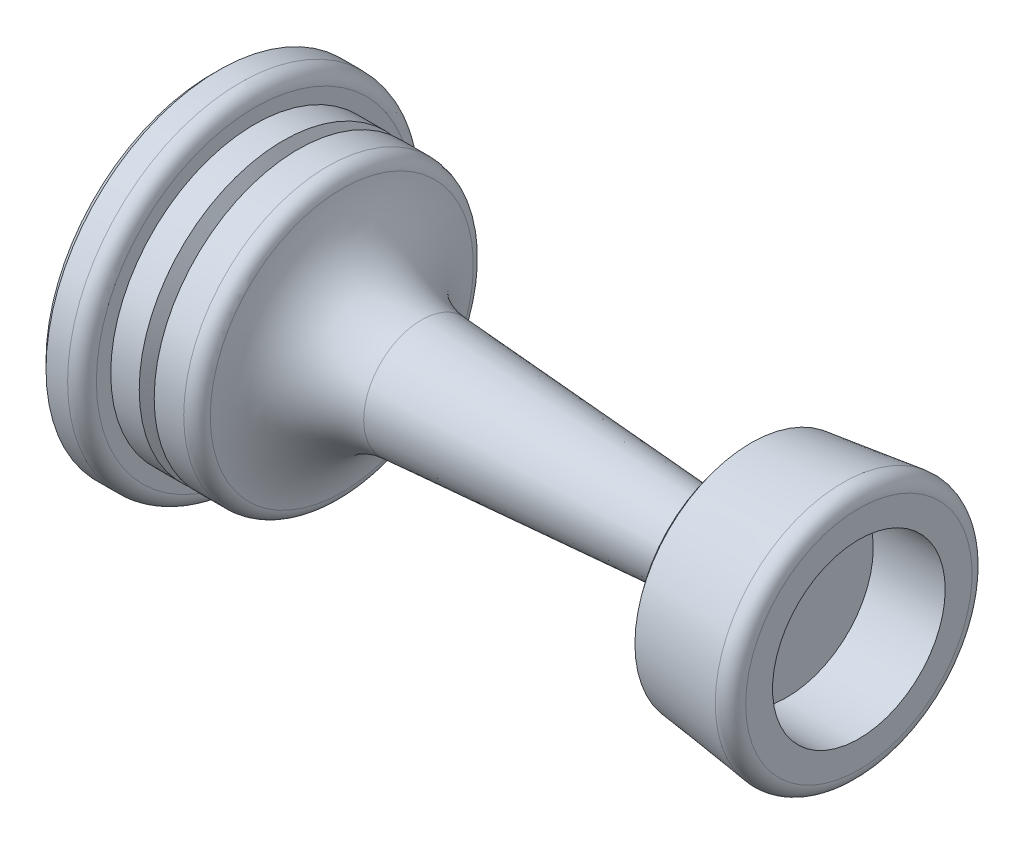
SolidWorks part; units mm, degrees
ref_plane "Front Plane" through (0, 0, 0) normal (0, 0, 1) x (1, 0, 0)
ref_plane "Top Plane" through (0, 0, 0) normal (0, 1, 0) x (1, 0, 0)
ref_plane "Right Plane" through (0, 0, 0) normal (1, 0, 0) x (0, 0, -1)
sketch "Sketch1" plane through (0, 0, 0) normal (0, 0, 1) x (1, 0, 0)
  line L0 (0, 0) -> (0, 11.5)
  line L1 (0.5, 12) -> (2, 12)
  line L2 (3, 11) -> (3, 10)
  line L3 (3, 10) -> (8.0718, 10)
  line L4 (14.5956, 4.0136) -> (37, 2.5)
  line L5 (37, 2.5) -> (37, 8)
  line L6 (37, 8) -> (45, 9)
  line L7 (0, 0) -> (45, 0)
  line L8 (0, 0) -> (-16.2845, 0) construction
  line L9 (45, 0) -> (45, -26.6806) construction
  line L10 (45, 9) -> (45, 0)
  line L14 (0, 11.5) -> (0.5, 12)
  arc A0 (9.0615, 9.1429) -> (14.5956, 4.0136) centre (15, 10) ccw
  arc A2 (2, 12) -> (3, 11) centre (2, 11) cw
  arc A3 (8.0718, 10) -> (9.0615, 9.1429) centre (8.0718, 9) cw
  point P1 (0, 12)
  point P20 (3, 12)
  point P23 (9, 10)
  dimension "D8" = 9
  dimension "D13" = 6
  dimension "D14" = 1
  dimension "D2" = 24
  dimension "D3" = 3
  dimension "D4" = 20
  dimension "D5" = 6
  dimension "D6" = 5
  dimension "D7" = 45
  dimension "D9" = 8
  dimension "D12" = 8
revolve "Revolve1" add sketch "Sketch1" angle 360 about L7
sketch "Sketch2" plane through (0, 0, 0) normal (0, 0, 1) x (1, 0, 0)
  line L0 (4.9794, 10) -> (5.5, 9)
  line L1 (8.0718, 10) -> (3, 10) construction
  line L2 (5.5, 9) -> (6.0206, 10)
  line L3 (4.9794, 10) -> (6.0206, 10)
  line L4 (5.5, 9) -> (5.5, 10) construction
  line L5 (3, -10) -> (3, 10) construction
  line L6 (0, 0) -> (11.1779, 0) construction
  dimension "D1" = 55
  dimension "D2" = 1
  dimension "D3" = 2.5
revolve "Cut-Revolve1" cut sketch "Sketch2" angle 360 about L6
sketch "Sketch3" plane through (0, 0, 0) normal (-1, 0, 0) x (0, 0, 1)
  circle A0 centre (0, 0) radius 6
  dimension "D1" = 12
extrude "Cut-Extrude1" cut sketch "Sketch3" against normal blind 5
sketch "Sketch4" plane through (45, 0, 0) normal (1, 0, 0) x (0, 0, -1)
  circle A0 centre (0, 0) radius 6
  dimension "D1" = 12
extrude "Cut-Extrude2" cut sketch "Sketch4" against normal blind 5
fillet "Fillet1" radius 1 1 edges at (45, 0, 9)
chamfer "Chamfer1" distance 0.5 angle 45 1 edges at (37, 0, 8)
